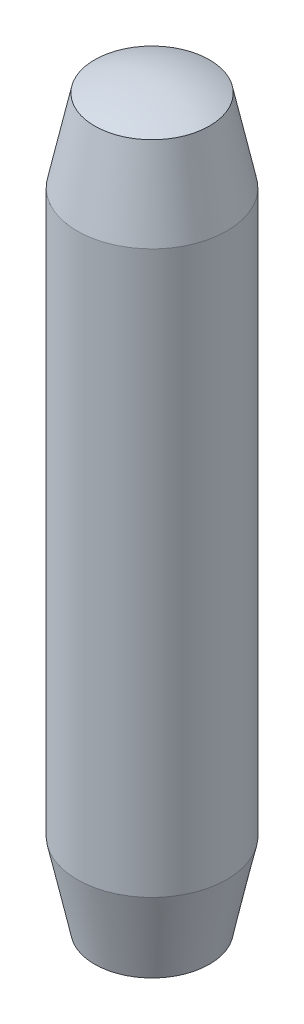
SolidWorks part; units mm, degrees
ref_plane "Front Plane" through (0, 0, 0) normal (0, 0, 1) x (1, 0, 0)
ref_plane "Top Plane" through (0, 0, 0) normal (0, 1, 0) x (1, 0, 0)
ref_plane "Right Plane" through (0, 0, 0) normal (1, 0, 0) x (0, 0, -1)
sketch "Sketch1" plane through (0, 0, 0) normal (0, 1, 0) x (1, 0, 0)
  circle A0 centre (0, 0) radius 0.4
  dimension "D1" = 0.8
extrude "Boss-Extrude1" add sketch "Sketch1" along normal blind 4
sketch "Sketch2" plane through (0, 0, 0) normal (0, 0, 1) x (1, 0, 0)
  line L0 (0, 0) -> (0, 4) construction
  line L1 (0.4, 4) -> (-0.4, 4) construction
  line L3 (0.4, 0) -> (0.4, 4) construction
  line L4 (0.4, 3.8928) -> (0, 3.8928) construction
  line L5 (0.4, 3.8928) -> (0.4, 4.1)
  line L7 (0, 4) -> (0, 4.1)
  line L8 (0.4, 4.1) -> (-0.4, 4.1)
  line L9 (0.4, 4.1) -> (0, 4.1)
  line L10 (0, 2) -> (1.533, 2) construction
  line L11 (0.4, 0.1072) -> (0, 0.1072) construction
  line L12 (0.4, -0.1) -> (0, -0.1)
  line L13 (0, 0) -> (0, -0.1)
  line L14 (0.4, 0.1072) -> (0.4, -0.1)
  arc A0 (0, 4) -> (0.4, 3.8928) centre (0, 3.2) cw
  arc A1 (0, 0) -> (0.4, 0.1072) centre (0, 0.8) ccw
  dimension "D1" = 0.8
  dimension "D2" = 0.1
revolve "Cut-Revolve2" cut sketch "Sketch2" angle 360 about L0
sketch "Sketch3" plane through (0, 0, 0) normal (0, 0, 1) x (1, 0, 0)
  line L0 (-0.4, 3.5) -> (-0.3067, 3.9389)
  line L1 (-0.4, 3.8928) -> (-0.4, 0.1072) construction
  line L2 (-0.4, 3.8928) -> (-0.4, 3.5)
  line L3 (0, 0) -> (0, 4) construction
  line L4 (0, 2) -> (0.4, 2) construction
  line L5 (0.4, 0.1072) -> (0.4, 3.8928) construction
  line L6 (-0.4, 0.1072) -> (-0.4, 0.5)
  line L7 (-0.4, 0.5) -> (-0.3067, 0.0611)
  arc A0 (0, 4) -> (-0.4, 3.8928) centre (0, 3.2) ccw construction
  arc A1 (-0.3067, 3.9389) -> (-0.4, 3.8928) centre (0, 3.2) ccw
  arc A2 (-0.3067, 0.0611) -> (-0.4, 0.1072) centre (0, 0.8) cw
  dimension "D1" = 12
  dimension "D2" = 0.5
revolve "Cut-Revolve3" cut sketch "Sketch3" angle 360 about L3
